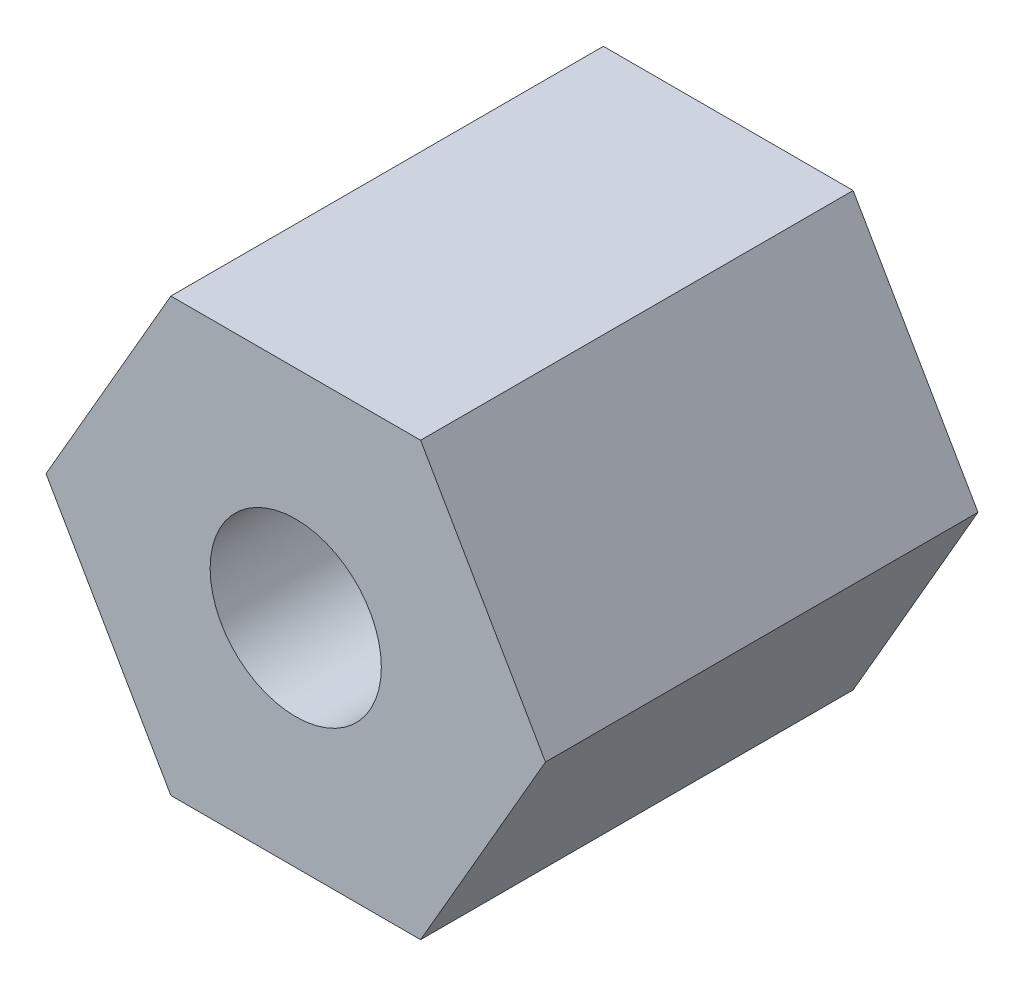
SolidWorks part; units mm, degrees
ref_plane "Front Plane" through (0, 0, 0) normal (0, 0, 1) x (1, 0, 0)
ref_plane "Top Plane" through (0, 0, 0) normal (0, 1, 0) x (1, 0, 0)
ref_plane "Right Plane" through (0, 0, 0) normal (1, 0, 0) x (0, 0, -1)
sketch "Sketch2" plane through (0, 0, 0) normal (0, 0, 1) x (1, 0, 0)
  line L0 (-5.5426, 0) -> (0, 0) construction
  line L1 (5.5426, 0) -> (2.7713, 4.8)
  line L2 (2.7713, 4.8) -> (-2.7713, 4.8)
  line L3 (-2.7713, 4.8) -> (-5.5426, 0)
  line L4 (-5.5426, 0) -> (-2.7713, -4.8)
  line L5 (-2.7713, -4.8) -> (2.7713, -4.8)
  line L6 (2.7713, -4.8) -> (5.5426, 0)
  circle A0 centre (0, 0) radius 4.8 construction
  dimension "D1" = 9.6
extrude "Boss-Extrude1" add sketch "Sketch2" along normal blind 9.6
sketch "Sketch3" plane through (0, 0, 0) normal (0, 0, -1) x (-1, 0, 0)
  circle A0 centre (0, 0) radius 1.9
  dimension "D1" = 3.8
extrude "Cut-Extrude1" cut sketch "Sketch3" against normal through all
